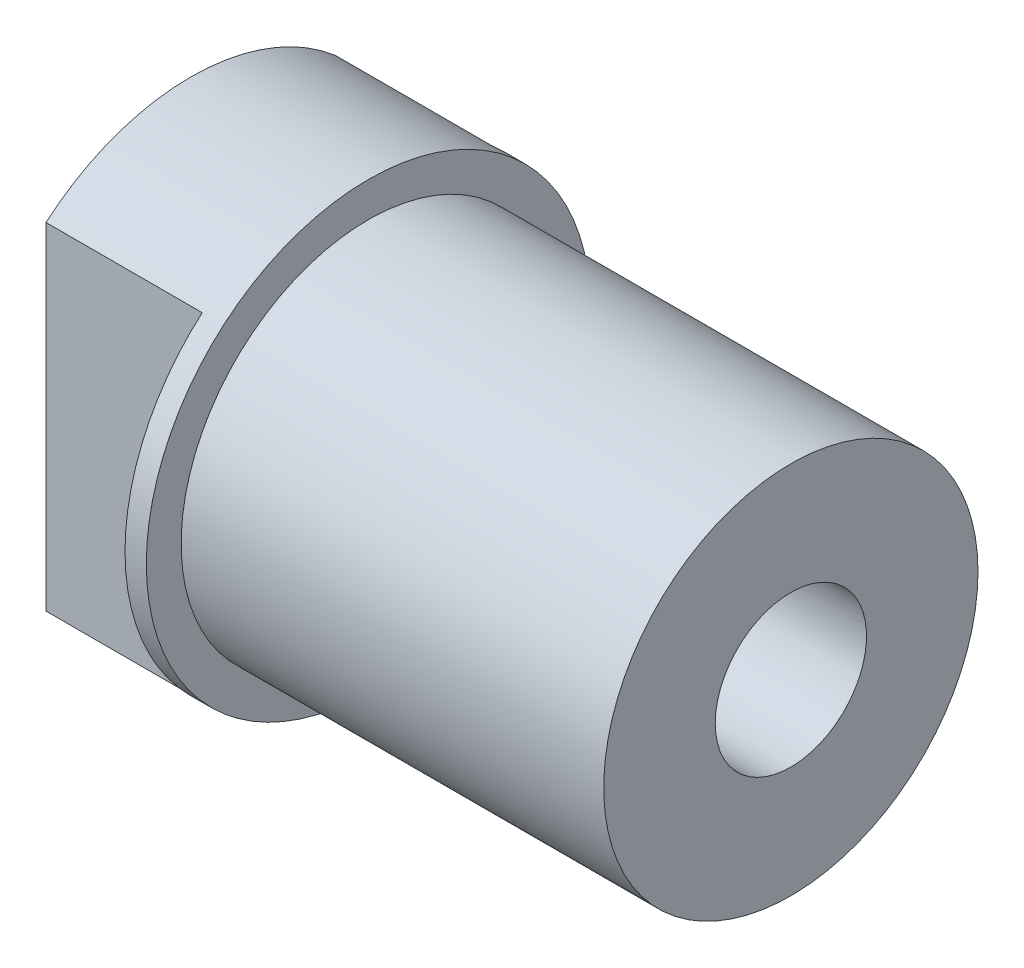
SolidWorks part; units mm, degrees
other "Markup1"
sketch "Sketch7" plane through (15.113, 7.9375, -7.9375) normal (0.8229, 0.5627, -0.0792) x (0.0116, -0.1561, -0.9877)
material "AISI 4130 Steel (McMaster EZ Weld Tubes)"
ref_plane "Top" through (0, 0, 0) normal (0, 0, 1) x (1, 0, 0)
ref_plane "Right" through (0, 0, 0) normal (0, 1, 0) x (1, 0, 0)
ref_plane "Front" through (0, 0, 0) normal (1, 0, 0) x (0, 0, -1)
sketch "Sketch2" plane through (0, 0, 0) normal (1, 0, 0) x (0, 0, -1)
  circle A0 centre (0, 0) radius 7.9375
  dimension "D1" = 15.875
extrude "Boss-Extrude1" add sketch "Sketch2" against normal blind 6.35
sketch "Sketch3" plane through (0, 0, 0) normal (1, 0, 0) x (0, 0, -1)
  circle A0 centre (0, 0) radius 6.6929
  circle A2 centre (0, 0) radius 7.9375 construction
  dimension "D1" = 1.2446
extrude "Boss-Extrude2" add sketch "Sketch3" along normal blind 15.113
sketch "Sketch4" plane through (0, 0, 0) normal (0, 1, 0) x (1, 0, 0)
  line L1 (-6.35, 7.9375) -> (-0.762, 7.9375)
  line L2 (-6.35, 7.9375) -> (-6.35, 5.1752)
  line L3 (-6.35, 5.1752) -> (-0.762, 5.1752)
  line L4 (-0.762, 7.9375) -> (-0.762, 5.1752)
  line L5 (-6.35, -7.9375) -> (-0.762, -7.9375)
  line L6 (-6.35, -7.9375) -> (-6.35, -5.1752)
  line L7 (-6.35, -5.1752) -> (-0.762, -5.1752)
  line L8 (-0.762, -7.9375) -> (-0.762, -5.1752)
  dimension "D1" = 10.3505
  dimension "D2" = 5.588
extrude "Cut-Extrude1" cut sketch "Sketch4" against normal mid plane 12.7
hole_wizard "1/4-28 Tapped Hole1" positions "3DSketch1" profile "Sketch5" tap size "1/4-28" standard "ANSI Inch" end condition through all
sketch3d "3DSketch1"
  arc A0 (-6.35, -6.0184, 5.1752) -> (-6.35, -6.0184, -5.1752) centre (-6.35, 0, 0) ccw construction
  arc A1 (-6.35, -6.0184, 5.1752) -> (-6.35, -6.0184, -5.1752) centre (-6.35, 0, 0) ccw
  point P1 (-6.35, 0, 0)
  point P4 (1.5875, 0, 0)
  point P5 (1.5875, 0, 0)
  point P9 (-6.35, 0, 0)
  point P12 (-6.35, 0, 0)
sketch "Sketch5" plane through (-6.35, 0, 0) normal (0, 1, 0) x (0, 0, 1)
  line L0 (0, 0) -> (0, 21.463)
  line L1 (0, 21.463) -> (2.7051, 21.463)
  line L2 (2.7051, 21.463) -> (2.7051, 0)
  line L5 (2.7051, 0) -> (0, 0)
  line L11 (0, -6.35) -> (0, 107.95) construction
  dimension "Thru Tap Drill Dia." = 5.4102
  dimension "Thru Tap Drill Depth" = 21.463
cosmetic thread "Hole Thread7" parameters "D2"=6.35
hole_wizard "5/16-24 Tapped Hole1" [suppressed] positions "3DSketch2" profile "Sketch6" tap size "5/16-24" standard "ANSI Inch"
sketch3d "3DSketch2"
  arc A0 (-6.35, -6.0184, 5.1752) -> (-6.35, -6.0184, -5.1752) centre (-6.35, 0, 0) ccw construction
  arc A1 (-6.35, -6.0184, 5.1752) -> (-6.35, -6.0184, -5.1752) centre (-6.35, 0, 0) ccw
  point P0 (-6.35, 0, 0)
  point P6 (1.5875, 0, 0)
  point P7 (1.5875, 0, 0)
sketch "Sketch6" plane through (-6.35, 0, 0) normal (0, 1, 0) x (0, 0, 1)
  line L0 (0, 0) -> (0, 21.463)
  line L1 (0, 21.463) -> (3.4544, 21.463)
  line L2 (3.4544, 21.463) -> (3.4544, 0)
  line L5 (3.4544, 0) -> (0, 0)
  line L11 (0, -6.35) -> (0, 107.95) construction
  dimension "Thru Tap Drill Dia." = 6.9088
  dimension "Thru Tap Drill Depth" = 21.463
cosmetic thread "Hole Thread8" [suppressed] parameters "D2"=7.9375
hole_wizard "M6x1.0 Tapped Hole1" [suppressed] positions "Sketch8" profile "Sketch9" tap size "M6x1.0" standard "ANSI Metric"
sketch "Sketch8" plane through (-6.35, 0, 0) normal (-1, 0, 0) x (0, 0, 1)
  point P0 (0, 0)
sketch "Sketch9" plane through (-6.35, 0, 0) normal (0, 1, 0) x (0, 0, 1)
  line L0 (0, 0) -> (0, 21.463)
  line L1 (0, 21.463) -> (2.5, 21.463)
  line L2 (2.5, 21.463) -> (2.5, 0)
  line L5 (2.5, 0) -> (0, 0)
  line L11 (0, -6.35) -> (0, 107.95) construction
  dimension "Thru Tap Drill Dia." = 5
  dimension "Thru Tap Drill Depth" = 21.463
cosmetic thread "Hole Thread9" [suppressed] parameters "D2"=6
equation "\"OD\"= 0.625"
equation "\"Wall\"= 0.049"
equation "\"D1@Sketch2\"=\"OD\""
equation "\"D1@Sketch3\"=\"Wall\""
